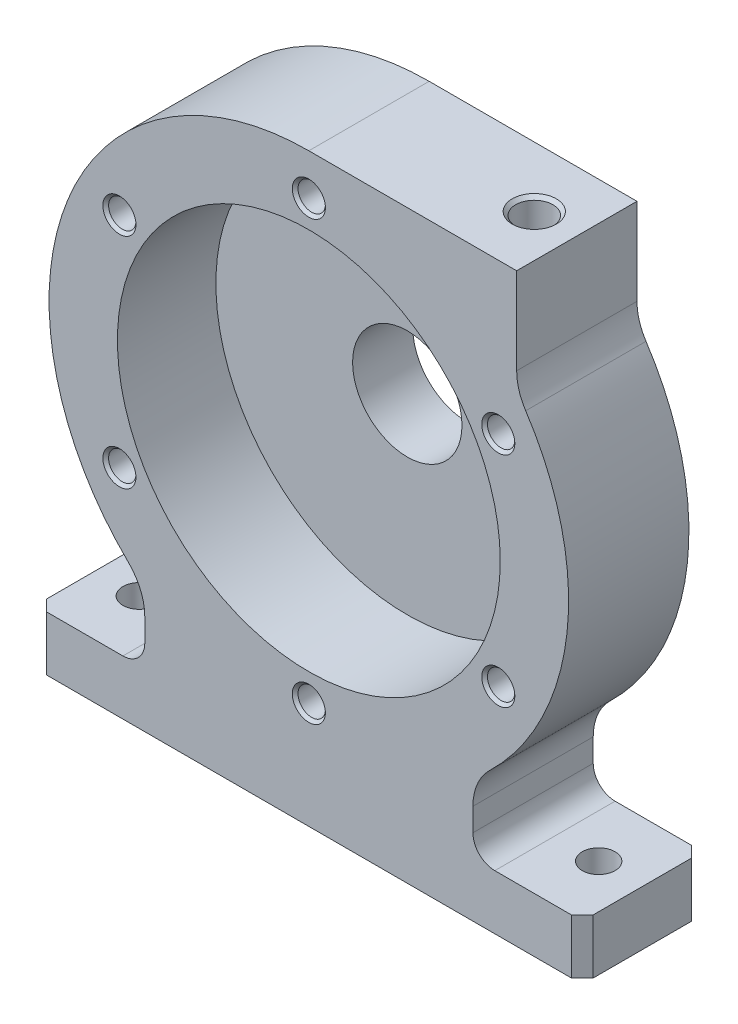
SolidWorks part; units mm, degrees
ref_plane "Front Plane" through (0, 0, 0) normal (0, 0, 1) x (1, 0, 0)
ref_plane "Top Plane" through (0, 0, 0) normal (0, 1, 0) x (1, 0, 0)
ref_plane "Right Plane" through (0, 0, 0) normal (1, 0, 0) x (0, 0, -1)
sketch "Sketch1" plane through (0, 0, 0) normal (0, 0, 1) x (1, 0, 0)
  line L0 (0, 0) -> (0, -59.5) construction
  line L1 (-50, -59.5) -> (50, -59.5)
  line L2 (50, -59.5) -> (50, -49.5)
  line L3 (50, -49.5) -> (34, -49.5)
  line L4 (30, -45.5) -> (30, -41.3068)
  line L5 (0, 47.5) -> (38, 47.5)
  line L6 (38, 47.5) -> (38, 31.6583)
  line L7 (-50, -59.5) -> (-50, -49.5)
  line L8 (-50, -49.5) -> (-34, -49.5)
  line L9 (-30, -45.5) -> (-30, -41.3068)
  arc A0 (0, 47.5) -> (-33.0435, -34.123) centre (0, 0) ccw
  arc A1 (33.0435, -34.123) -> (39.6522, 26.1525) centre (0, 0) ccw
  arc A2 (30, -41.3068) -> (33.0435, -34.123) centre (40, -41.3068) cw
  arc A3 (38, 31.6583) -> (39.6522, 26.1525) centre (48, 31.6583) ccw
  arc A4 (34, -49.5) -> (30, -45.5) centre (34, -45.5) cw
  arc A5 (-34, -49.5) -> (-30, -45.5) centre (-34, -45.5) ccw
  arc A6 (-30, -41.3068) -> (-33.0435, -34.123) centre (-40, -41.3068) ccw
  point P13 (30, -36.8273)
  dimension "D1" = 95
  dimension "D7" = 10
  dimension "D8" = 4
  dimension "D2" = 38
  dimension "D3" = 50
  dimension "D4" = 10
  dimension "D5" = 59.5
  dimension "D6" = 30
extrude "Boss-Extrude1" add sketch "Sketch1" along normal blind 22
sketch "Sketch2" plane through (0, 0, 22) normal (0, 0, 1) x (1, 0, 0)
  circle A0 centre (0, 0) radius 35
  dimension "D1" = 70
extrude "Cut-Extrude1" cut sketch "Sketch2" against normal blind 18
sketch "Sketch3" plane through (0, 0, 0) normal (0, 0, -1) x (-1, 0, 0)
  circle A0 centre (0, 0) radius 14
  dimension "D1" = 28
extrude "Boss-Extrude2" add sketch "Sketch3" along normal blind 7
fillet "Fillet1" radius 4 1 edges at (-14, 0, 0)
sketch "Sketch4" plane through (0, 0, -7) normal (0, 0, -1) x (-1, 0, 0)
  circle A0 centre (0, 0) radius 10
  dimension "D1" = 20
extrude "Cut-Extrude2" cut sketch "Sketch4" against normal through all
chamfer "Chamfer1" distance 2 angle 45 4 edges at (-50, -54.5, 0) (-50, -54.5, 22) (50, -54.5, 0) (50, -54.5, 22)
sketch "Sketch5" plane through (0, 47.5, 0) normal (0, 1, 0) x (1, 0, 0)
  line L0 (38, -11) -> (0, -11) construction
  line L1 (38, -22) -> (38, 0) construction
  line L2 (0, -22) -> (0, 0) construction
hole_wizard "M8x1.25 Tapped Hole1" positions "Sketch6" profile "Sketch7" tap size "M8x1.25" standard "ANSI Metric"
sketch "Sketch6" plane through (0, 47.5, 0) normal (0, 1, 0) x (1, 0, 0)
  line L0 (38, -11) -> (0, -11) construction
  line L1 (38, -22) -> (38, 0) construction
  point P0 (30.2242, -11)
  dimension "D1" = 7.7759
sketch "Sketch7" plane through (30.2242, 47.5, 11) normal (1, 0, 0) x (0, 0, 1)
  line L0 (0, 0) -> (0, 31.7929)
  line L1 (0, 31.7929) -> (3.4, 29.75)
  line L2 (3.4, 29.75) -> (3.4, 0.625)
  line L3 (3.4, 0.625) -> (4.025, 0)
  line L5 (4.025, 0) -> (0, 0)
  line L6 (-3.4, 0.625) -> (-4.025, 0) construction
  line L10 (0, 31.7929) -> (-3.4, 29.75) construction
  line L11 (0, -6.35) -> (0, 107.95) construction
  dimension "Tap Drill Dia." = 6.8
  dimension "Tap Drill Depth" = 29.75
  dimension "Near C'Sink Dia." = 8.05
  dimension "Near C'Sink Angle" = 90
  dimension "Drill Angle" = 118
cosmetic thread "Hole Thread1" parameters "D1"=16, "D2"=8
sketch "Sketch8" plane through (0, 0, 22) normal (0, 0, 1) x (1, 0, 0)
  circle A0 centre (0, 0) radius 40 construction
  dimension "D1" = 80
hole_wizard "M6x1.0 Tapped Hole1" positions "Sketch9" profile "Sketch10" tap size "M6x1.0" standard "ANSI Metric"
sketch "Sketch9" plane through (0, 0, 22) normal (0, 0, 1) x (1, 0, 0)
  circle A0 centre (0, 0) radius 40 construction
  point P0 (0, 40)
sketch "Sketch10" plane through (0, 40, 22) normal (1, 0, 0) x (0, -1, 0)
  line L0 (0, 0) -> (0, 16.5022)
  line L1 (0, 16.5022) -> (2.5, 15)
  line L2 (2.5, 15) -> (2.5, 0.525)
  line L3 (2.5, 0.525) -> (3.025, 0)
  line L5 (3.025, 0) -> (0, 0)
  line L6 (-2.5, 0.525) -> (-3.025, 0) construction
  line L10 (0, 16.5022) -> (-2.5, 15) construction
  line L11 (0, -6.35) -> (0, 107.95) construction
  dimension "Tap Drill Dia." = 5
  dimension "Tap Drill Depth" = 15
  dimension "Near C'Sink Dia." = 6.05
  dimension "Near C'Sink Angle" = 90
  dimension "Drill Angle" = 118
cosmetic thread "Hole Thread2" parameters "D1"=12, "D2"=6
pattern_circular "CirPattern1" count 6 over 360 about axis through (0, 0, 0) along (0, 0, 1) of "M6x1.0 Tapped Hole1"
hole_wizard "CSK for M8 Countersunk Flat Head Screw1" positions "Sketch11" profile "Sketch12" countersink size "M8" standard "ISO"
sketch "Sketch11" plane through (0, -59.5, 0) normal (0, -1, 0) x (-1, 0, 0)
  line L0 (-50, -20) -> (-50, -2) construction
  line L1 (50, -20) -> (50, -2) construction
  point P0 (42, -11)
  point P2 (-42, -11)
  point P10 (50, -11)
  point P11 (-50, -11)
  dimension "D1" = 8
  dimension "D2" = 8
sketch "Sketch12" plane through (-42, -59.5, 11) normal (1, 0, 0) x (0, 0, -1)
  line L0 (0, 0) -> (0, 21.8026)
  line L1 (0, 21.8026) -> (3, 20)
  line L2 (3, 20) -> (3, 1)
  line L3 (3, 1) -> (4, 0)
  line L5 (4, 0) -> (0, 0)
  line L6 (-3, 1) -> (-4, 0) construction
  line L10 (0, 21.8026) -> (-3, 20) construction
  line L11 (0, -6.35) -> (0, 107.95) construction
  dimension "Hole Dia." = 6
  dimension "Hole Depth" = 20
  dimension "Near C'Sink Dia." = 8
  dimension "Near C'Sink Angle" = 90
  dimension "Drill Angle" = 118
